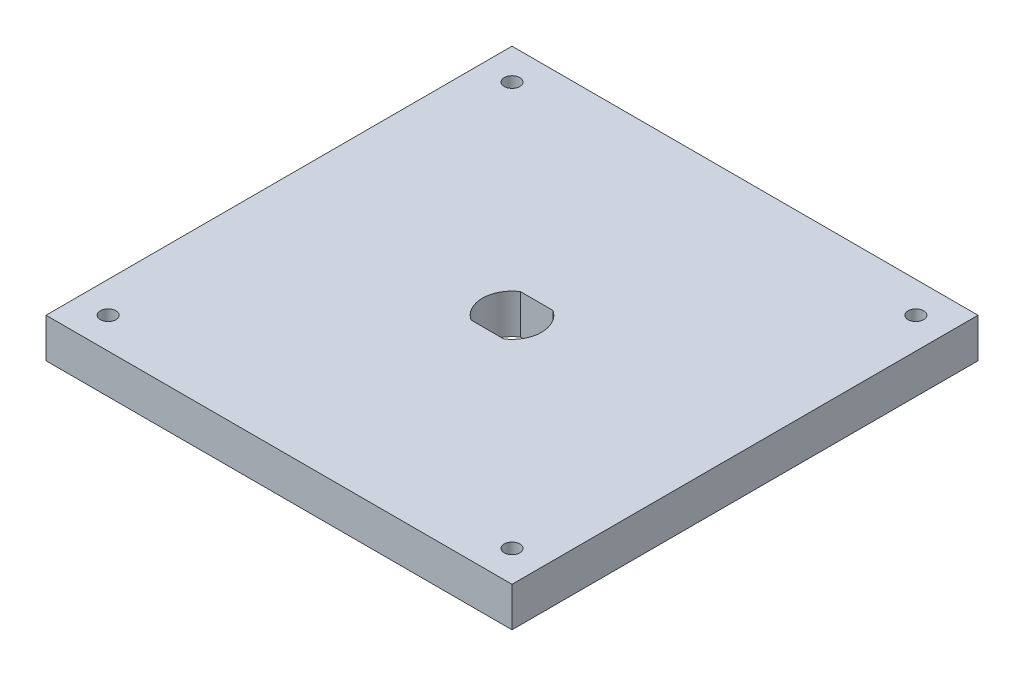
SolidWorks part; units mm, degrees
ref_plane "Front Plane" through (0, 0, 0) normal (0, 0, 1) x (1, 0, 0)
ref_plane "Top Plane" through (0, 0, 0) normal (0, 1, 0) x (1, 0, 0)
ref_plane "Right Plane" through (0, 0, 0) normal (1, 0, 0) x (0, 0, -1)
sketch "Sketch1" plane through (0, 0, 0) normal (0, 1, 0) x (1, 0, 0)
  line L1 (0, 0) -> (150, 0)
  line L2 (0, 0) -> (0, 150)
  line L3 (0, 150) -> (150, 150)
  line L4 (150, 0) -> (150, 150)
  dimension "D1" = 150
  dimension "D2" = 150
extrude "Boss-Extrude1" add sketch "Sketch1" along normal blind 12.7
sketch "Sketch2" plane through (0, 12.7, 0) normal (0, 1, 0) x (1, 0, 0)
  line L0 (75, 150) -> (75, 0) construction
  line L1 (150, 150) -> (0, 150) construction
  line L2 (0, 0) -> (150, 0) construction
  line L3 (0, 75) -> (150, 75) construction
  line L4 (0, 150) -> (0, 0) construction
  line L5 (150, 0) -> (150, 150) construction
  line L7 (84.525, 75) -> (65.475, 75)
  line L8 (84.525, 75) -> (84.525, 90.875)
  line L9 (84.525, 90.875) -> (65.475, 90.875)
  line L10 (65.475, 75) -> (65.475, 90.875)
  line L11 (69.7349, 82.9375) -> (80.2651, 82.9375)
  line L12 (69.7349, 82.9375) -> (69.7349, 67.0625)
  line L13 (69.7349, 67.0625) -> (80.2651, 67.0625)
  line L14 (80.2651, 82.9375) -> (80.2651, 67.0625)
  line L15 (69.7349, 82.9375) -> (80.2651, 67.0625) construction
  line L16 (69.7349, 67.0625) -> (80.2651, 82.9375) construction
  circle A0 centre (75, 75) radius 9.525
  circle A1 centre (10, 140) radius 2.5
  circle A2 centre (140, 140) radius 2.5
  circle A3 centre (140, 10) radius 2.5
  circle A4 centre (10, 10) radius 2.5
  point P22 (75, 67.0625)
  dimension "D1" = 19.05
  dimension "D5" = 5
  dimension "D2" = 19.05
  dimension "D3" = 7.9375
  dimension "D4" = 23.8125
  dimension "D6" = 10
  dimension "D7" = 10
extrude "Cut-Extrude1" cut sketch "Sketch2" against normal blind 12.7 contours L7 A0 L14 | L12 A0 L7 | L14 L11 L12 L7 | L14 A0 L7 | L7 A0 L12 | L14 L7 L12 L13 | A1 | A2 | A3 | A4
